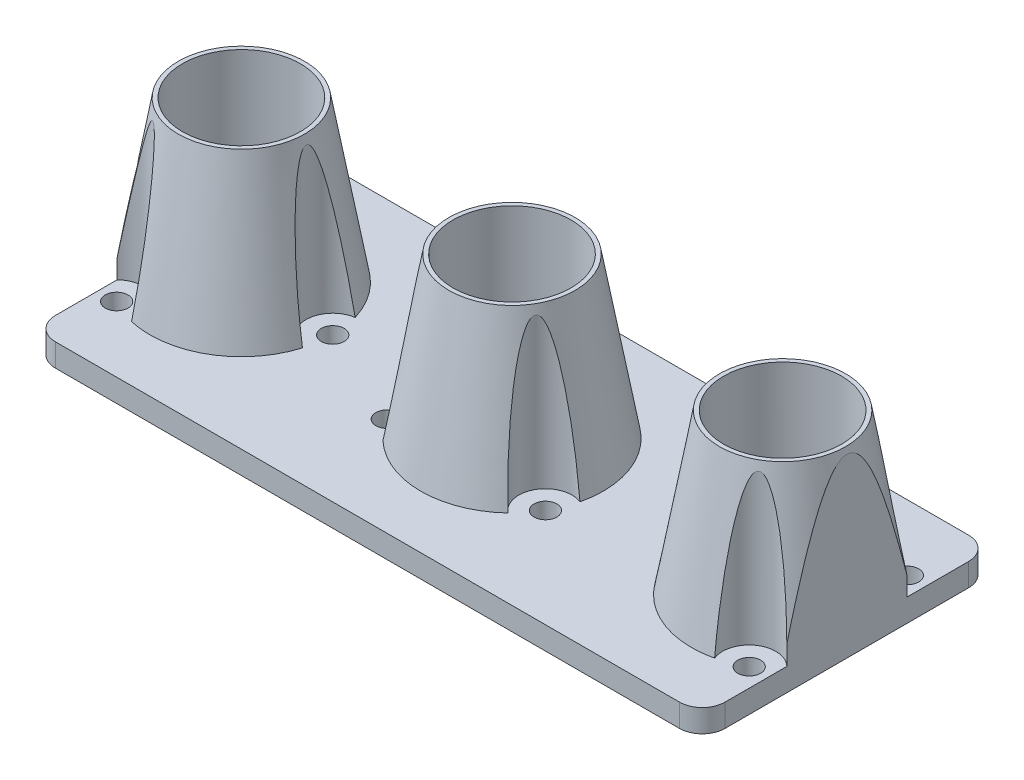
SolidWorks part; units mm, degrees
ref_plane "Front Plane" through (0, 0, 0) normal (0, 0, 1) x (1, 0, 0)
ref_plane "Top Plane" through (0, 0, 0) normal (0, 1, 0) x (1, 0, 0)
ref_plane "Right Plane" through (0, 0, 0) normal (1, 0, 0) x (0, 0, -1)
sketch "Sketch1" plane through (0, 0, 0) normal (0, 1, 0) x (1, 0, 0)
  line L0 (-64.0914, 0) -> (72.7034, 0) construction
  line L1 (-44.5, 19.5) -> (44.5, 19.5) construction
  line L2 (-44.5, 19.5) -> (-44.5, -19.5) construction
  line L3 (-44.5, -19.5) -> (44.5, -19.5) construction
  line L4 (44.5, 19.5) -> (44.5, -19.5) construction
  line L5 (-44.5, 19.5) -> (44.5, -19.5) construction
  line L6 (-44.5, -19.5) -> (44.5, 19.5) construction
  line L7 (0, 34.1732) -> (0, -36.3857) construction
  line L8 (41, 19) -> (-41, 19)
  line L9 (-44, 16) -> (-44, -16)
  line L10 (44, 16) -> (44, -16)
  line L11 (41, -19) -> (-41, -19)
  circle A0 centre (-35.56, 0) radius 7.75
  circle A1 centre (0, 0) radius 7.75
  arc A4 (-41, 19) -> (-44, 16) centre (-41, 16) ccw
  circle A6 centre (35.56, 0) radius 7.75
  arc A7 (41, 19) -> (44, 16) centre (41, 16) cw
  arc A9 (41, -19) -> (44, -16) centre (41, -16) ccw
  arc A14 (-41, -19) -> (-44, -16) centre (-41, -16) cw
  circle A16 centre (-23.56, 0) radius 1.5
  circle A17 centre (-41.56, -10.3923) radius 1.5
  circle A18 centre (-41.56, 10.3923) radius 1.5
  circle A19 centre (41.56, -10.3923) radius 1.5
  circle A20 centre (23.56, 0) radius 1.5
  circle A21 centre (41.56, 10.3923) radius 1.5
  circle A22 centre (0, 12) radius 1.5
  circle A23 centre (10.3923, -6) radius 1.5
  circle A24 centre (-10.3923, -6) radius 1.5
  point P0 (0, 0)
  point P29 (0, 19)
  point P35 (44, 0)
  point P48 (-44, 0)
  dimension "D3" = 15.5
  dimension "D7" = 3
  dimension "D10" = 3
  dimension "D9" = 3
  dimension "D1" = 39
  dimension "D2" = 89
  dimension "D4" = 35.56
  dimension "D5" = 1
  dimension "D6" = 1
  dimension "D8" = 12
  dimension "D11" = 12
  dimension "D12" = 3
extrude "Boss-Extrude1" add sketch "Sketch1" along normal blind 3
sketch "Sketch2" plane through (0, 3, 0) normal (0, 1, 0) x (1, 0, 0)
  circle A0 centre (-35.56, 0) radius 12
  circle A1 centre (0, 0) radius 12
  circle A2 centre (35.56, 0) radius 12
  dimension "D1" = 24
extrude "Boss-Extrude2" add sketch "Sketch2" along normal blind 21 draft 10
sketch "Sketch4" plane through (0, 3, 0) normal (0, 1, 0) x (1, 0, 0)
  circle A0 centre (-35.56, 0) radius 7.75
  circle A1 centre (0, 0) radius 7.75
  circle A2 centre (35.56, 0) radius 7.75
  circle A3 centre (-41.56, 10.3923) radius 3.5
  circle A4 centre (-23.56, 0) radius 3.5
  circle A5 centre (-41.56, -10.3923) radius 3.5
  circle A6 centre (0, 12) radius 3.5
  circle A7 centre (-10.3923, -6) radius 3.5
  circle A8 centre (10.3923, -6) radius 3.5
  circle A9 centre (23.56, 0) radius 3.5
  circle A10 centre (41.56, 10.3923) radius 3.5
  circle A11 centre (41.56, -10.3923) radius 3.5
  circle A13 centre (-35.56, 0) radius 7.75 construction
  dimension "D1" = 7
extrude "Cut-Extrude1" cut sketch "Sketch4" along normal up to surface (21 mm away) up to face at (-35.56, 24, 8.2971)
sketch "Sketch5" plane through (0, 3, 0) normal (0, 1, 0) x (1, 0, 0)
  line L0 (-44, 16) -> (-44, -16) construction
  line L1 (-44, 19) -> (44, 19)
  line L2 (-44, 19) -> (-44, -19)
  line L3 (-44, -19) -> (44, -19)
  line L4 (44, 19) -> (44, -19)
  line L5 (44, 16) -> (44, -16) construction
  line L6 (41, -19) -> (-41, -19) construction
  line L7 (41, 19) -> (-41, 19) construction
extrude "Cut-Extrude2" cut sketch "Sketch5" along normal through all flip side to cut
